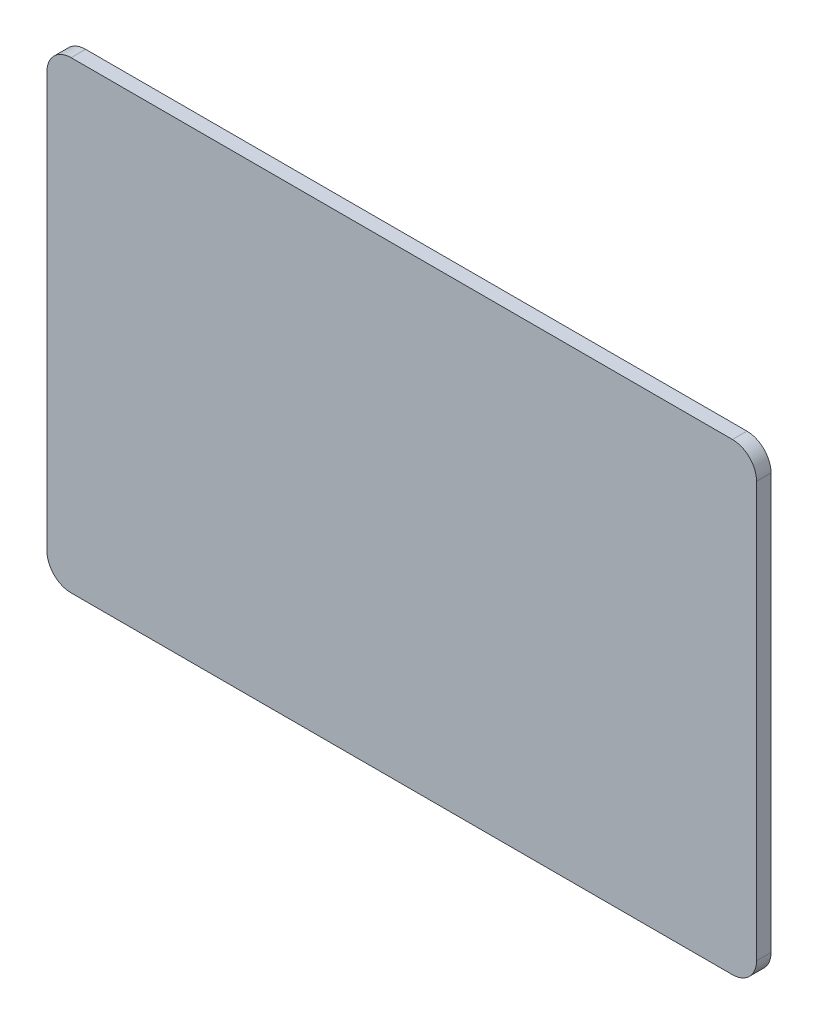
SolidWorks part; units mm, degrees
ref_plane "前视基准面" through (0, 0, 0) normal (0, 0, 1) x (1, 0, 0)
ref_plane "上视基准面" through (0, 0, 0) normal (0, 1, 0) x (1, 0, 0)
ref_plane "右视基准面" through (0, 0, 0) normal (1, 0, 0) x (0, 0, -1)
sketch "草图2" plane through (0, 0, 0) normal (0, 0, 1) x (1, 0, 0)
  line L1 (-1075.5484, 479.9927) -> (293.9743, 479.9927)
  line L2 (-1125.5484, 429.9927) -> (-1125.5484, -429.9927)
  line L3 (-1075.5484, -479.9927) -> (293.9743, -479.9927)
  line L4 (343.9743, 429.9927) -> (343.9743, -429.9927)
  line L5 (-1125.5484, 479.9927) -> (343.9743, -479.9927) construction
  line L6 (-1125.5484, -479.9927) -> (343.9743, 479.9927) construction
  arc A0 (293.9743, 479.9927) -> (343.9743, 429.9927) centre (293.9743, 429.9927) cw
  arc A1 (-1125.5484, -429.9927) -> (-1075.5484, -479.9927) centre (-1075.5484, -429.9927) ccw
  arc A2 (-1075.5484, 479.9927) -> (-1125.5484, 429.9927) centre (-1075.5484, 429.9927) ccw
  arc A3 (293.9743, -479.9927) -> (343.9743, -429.9927) centre (293.9743, -429.9927) ccw
  point P0 (-390.787, 0)
  dimension "D1" = 50
extrude "凸台-拉伸1" add sketch "草图2" along normal blind 30
sketch "草图4" plane through (0, 0, 0) normal (0, 0, -1) x (-1, 0, 0)
  line L1 (510, 200) -> (810, 200)
  line L2 (460, 150) -> (460, -150)
  line L3 (510, -200) -> (810, -200)
  line L4 (860, 150) -> (860, -150)
  line L5 (460, 200) -> (860, -200) construction
  line L6 (460, -200) -> (860, 200) construction
  arc A0 (810, 200) -> (860, 150) centre (810, 150) cw
  arc A1 (460, -150) -> (510, -200) centre (510, -150) ccw
  arc A2 (510, 200) -> (460, 150) centre (510, 150) ccw
  arc A3 (810, -200) -> (860, -150) centre (810, -150) ccw
  point P0 (660, 0)
  dimension "D4" = 50
  dimension "D1" = 400
  dimension "D2" = 400
  dimension "D3" = 660
extrude "凸台-拉伸2" add sketch "草图4" along normal blind 100
ref_plane "基准面1" through (0, 0, -250) normal (0, 0, -1) x (-1, 0, 0)
sketch "草图5" plane through (0, 0, -250) normal (0, 0, -1) x (-1, 0, 0)
  circle A0 centre (660, 0) radius 266.9159
